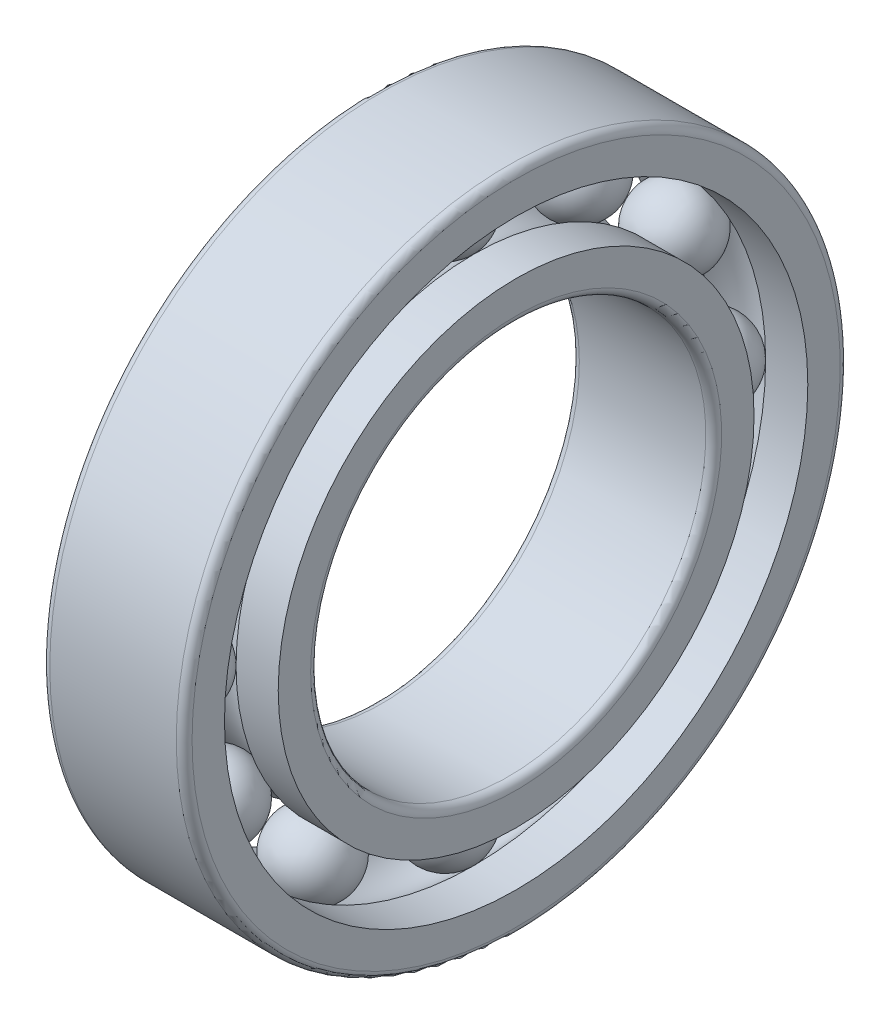
SolidWorks part; units mm, degrees
material "Литая легированная сталь"
ref_plane "Спереди" through (0, 0, 0) normal (0, 0, 1) x (1, 0, 0)
ref_plane "Сверху" through (0, 0, 0) normal (0, 1, 0) x (1, 0, 0)
ref_plane "Справа" through (0, 0, 0) normal (1, 0, 0) x (0, 0, -1)
sketch "Эскиз1" plane through (0, 0, 0) normal (0, 0, 1) x (1, 0, 0)
  line L0 (0, 0) -> (13979.1977, 0) construction
  line L1 (0, 15.05) -> (0, 12.5)
  line L2 (0, 12.5) -> (9, 12.5)
  line L3 (9, 12.5) -> (9, 15.05)
  line L6 (9, 18.45) -> (9, 21)
  line L7 (9, 21) -> (0, 21)
  line L8 (0, 21) -> (0, 18.45)
  line L9 (0, 12.5) -> (9, 21) construction
  line L10 (0, 21) -> (9, 12.5) construction
  line L11 (0, 18.45) -> (2.667, 18.45)
  line L12 (6.333, 18.45) -> (9, 18.45)
  line L13 (0, 15.05) -> (2.667, 15.05)
  line L14 (6.333, 15.05) -> (9, 15.05)
  arc A0 (2.667, 18.45) -> (6.333, 18.45) centre (4.5, 16.75) cw
  arc A1 (2.667, 15.05) -> (6.333, 15.05) centre (4.5, 16.75) ccw
  dimension "D5" = 2.5
  dimension "D1" = 42
  dimension "D2" = 9
  dimension "D3" = 25
  dimension "D4" = 2.55
revolve "Повернуть1" add sketch "Эскиз1" angle 360 about L0
fillet "Скругление1" radius 0.5 2 edges at (9, 0, 21) (0, 0, 21)
fillet "Скругление2" radius 0.5 2 edges at (9, 0, 12.5) (0, 0, 12.5)
sketch "Эскиз2" plane through (0, 0, 0) normal (0, 0, 1) x (1, 0, 0)
  line L0 (2.667, 15.05) -> (6.333, 18.45) construction
  line L1 (2.667, 18.45) -> (6.333, 15.05) construction
  line L2 (2, 16.75) -> (7, 16.75) construction
  line L3 (2, 16.75) -> (7, 16.75)
  arc A0 (7, 16.75) -> (2, 16.75) centre (4.5, 16.75) ccw
  dimension "D2" = 2.5
  dimension "D1" = 5
revolve "Повернуть4" add sketch "Эскиз2" angle 360 about L2
pattern_circular "Круговой массив1" count 12 over 360 about axis through (0, 0, 0) along (1, 0, 0) of bodies 105
